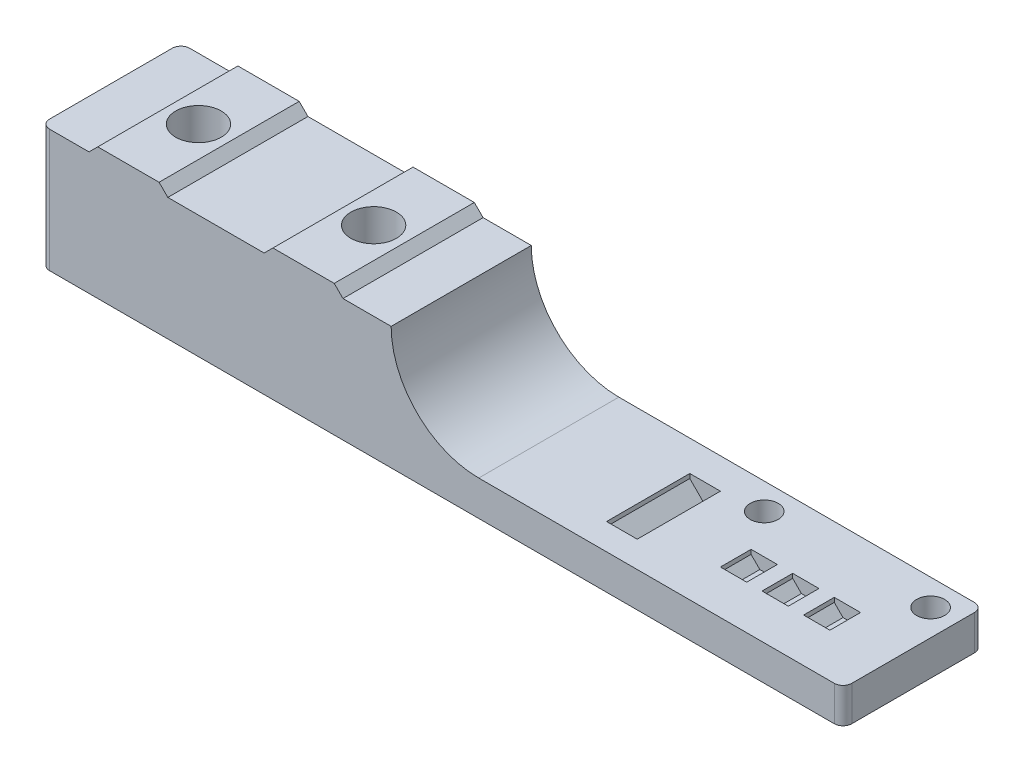
SolidWorks part; units mm, degrees
ref_plane "Front Plane" through (0, 0, 0) normal (0, 0, 1) x (1, 0, 0)
ref_plane "Top Plane" through (0, 0, 0) normal (0, 1, 0) x (1, 0, 0)
ref_plane "Right Plane" through (0, 0, 0) normal (1, 0, 0) x (0, 0, -1)
sketch "Sketch1" plane through (0, 0, 0) normal (0, 0, 1) x (1, 0, 0)
  line L0 (0, 0) -> (91.6, 0)
  line L1 (91.6, 0) -> (91.6, 4)
  line L2 (91.6, 4) -> (50, 4)
  line L3 (25.5, 14) -> (14.5, 14)
  line L4 (40, 14) -> (34.5, 14)
  line L5 (0, 14) -> (0, 0)
  line L6 (5.5, 14) -> (6.5, 15)
  line L7 (6.5, 15) -> (13.5, 15)
  line L8 (13.5, 15) -> (14.5, 14)
  line L9 (25.5, 14) -> (26.5, 15)
  line L10 (26.5, 15) -> (33.5, 15)
  line L11 (33.5, 15) -> (34.5, 14)
  line L12 (5.5, 14) -> (0, 14)
  arc A0 (40, 14) -> (50, 4) centre (50, 14) ccw
  dimension "D13" = 20
  dimension "D1" = 91.6
  dimension "D2" = 14
  dimension "D3" = 40
  dimension "D4" = 4
  dimension "D5" = 1
  dimension "D6" = 1
  dimension "D7" = 45
  dimension "D8" = 45
  dimension "D9" = 9
  dimension "D10" = 11
  dimension "D11" = 9
  dimension "D12" = 5.5
extrude "Boss-Extrude1" add sketch "Sketch1" against normal blind 16
sketch "Sketch2" plane through (0, 15, 0) normal (0, 1, 0) x (1, 0, 0)
  line L0 (33.5, 16) -> (26.5, 16) construction
  line L1 (13.5, 16) -> (6.5, 16) construction
  line L2 (5.5, 16) -> (5.5, 0) construction
  line L4 (25.5, 16) -> (25.5, 0) construction
  circle A0 centre (10, 8) radius 2.6
  circle A1 centre (30, 8) radius 2.6
  dimension "D1" = 5.2
  dimension "D2" = 5.2
  dimension "D3" = 8
  dimension "D4" = 8
  dimension "D5" = 4.5
  dimension "D6" = 4.5
extrude "Cut-Extrude1" cut sketch "Sketch2" against normal blind 4.8
sketch "Sketch3" plane through (0, 0, 0) normal (0, -1, 0) x (1, 0, 0)
  line L0 (0, -16) -> (0, 0) construction
  line L1 (0, -16) -> (91.6, -16) construction
  circle A0 centre (10, -8) radius 4.5
  circle A1 centre (30, -8) radius 4.5
  dimension "D1" = 9
  dimension "D2" = 9
  dimension "D3" = 10
  dimension "D4" = 20
  dimension "D5" = 8
extrude "Cut-Extrude2" cut sketch "Sketch3" against normal blind 10
sketch "Sketch4" plane through (0, 0, 0) normal (0, -1, 0) x (1, 0, 0)
  line L0 (0, -16) -> (91.6, -16) construction
  line L1 (91.6, -16) -> (91.6, 0) construction
  circle A0 centre (88.6, -13) radius 1.6
  circle A1 centre (69.6, -13) radius 1.6
  dimension "D1" = 3.2
  dimension "D2" = 3.2
  dimension "D3" = 3
  dimension "D4" = 3
  dimension "D5" = 19
extrude "Cut-Extrude3" cut sketch "Sketch4" against normal up to next
sketch "Sketch5" plane through (0, 4, 0) normal (0, 1, 0) x (1, 0, 0)
  line L0 (91.6, 16) -> (91.6, 0) construction
  line L1 (72.6, 5) -> (75.6, 5)
  line L2 (72.6, 5) -> (72.6, 8.5)
  line L3 (72.6, 8.5) -> (75.6, 8.5)
  line L4 (75.6, 5) -> (75.6, 8.5)
  line L5 (77.35, 5) -> (80.35, 5)
  line L6 (77.35, 5) -> (77.35, 8.5)
  line L7 (77.35, 8.5) -> (80.35, 8.5)
  line L8 (80.35, 5) -> (80.35, 8.5)
  line L9 (82.1, 5) -> (85.1, 5)
  line L10 (82.1, 5) -> (82.1, 8.5)
  line L11 (82.1, 8.5) -> (85.1, 8.5)
  line L12 (85.1, 5) -> (85.1, 8.5)
  line L13 (91.6, 16) -> (50, 16) construction
  dimension "D1" = 1.75
  dimension "D2" = 1.75
  dimension "D3" = 6.5
  dimension "D4" = 7.5
  dimension "D5" = 3
  dimension "D6" = 3
  dimension "D7" = 3
  dimension "D8" = 3.5
  dimension "D9" = 3.5
  dimension "D10" = 3.5
  dimension "D11" = 7.5
  dimension "D12" = 7.5
extrude "Cut-Extrude4" cut sketch "Sketch5" against normal blind 1.5
chamfer "Chamfer1" distance 1 angle 45 6 edges at (72.6, 2.5, -6.75) (77.35, 2.5, -6.75) (82.1, 2.5, -6.75) (85.1, 2.5, -6.75) (80.35, 2.5, -6.75) (75.6, 2.5, -6.75)
sketch "Sketch6" plane through (0, 4, 0) normal (0, 1, 0) x (1, 0, 0)
  line L0 (91.6, 0) -> (50, 0) construction
  line L1 (65.1, 12.5) -> (61.6, 12.5)
  line L2 (65.1, 12.5) -> (65.1, 3)
  line L3 (65.1, 3) -> (61.6, 3)
  line L4 (61.6, 12.5) -> (61.6, 3)
  line L6 (91.6, 16) -> (91.6, 0) construction
  dimension "D1" = 3.5
  dimension "D2" = 9.5
  dimension "D3" = 3
  dimension "D4" = 26.5
extrude "Cut-Extrude5" cut sketch "Sketch6" against normal blind 2
chamfer "Chamfer2" distance 1.5 angle 45 2 edges at (61.6, 2, -7.75) (65.1, 2, -7.75)
fillet "Fillet1" radius 1 4 edges at (0, 7, -16) (0, 7, 0) (91.6, 2, -16) (91.6, 2, 0)
